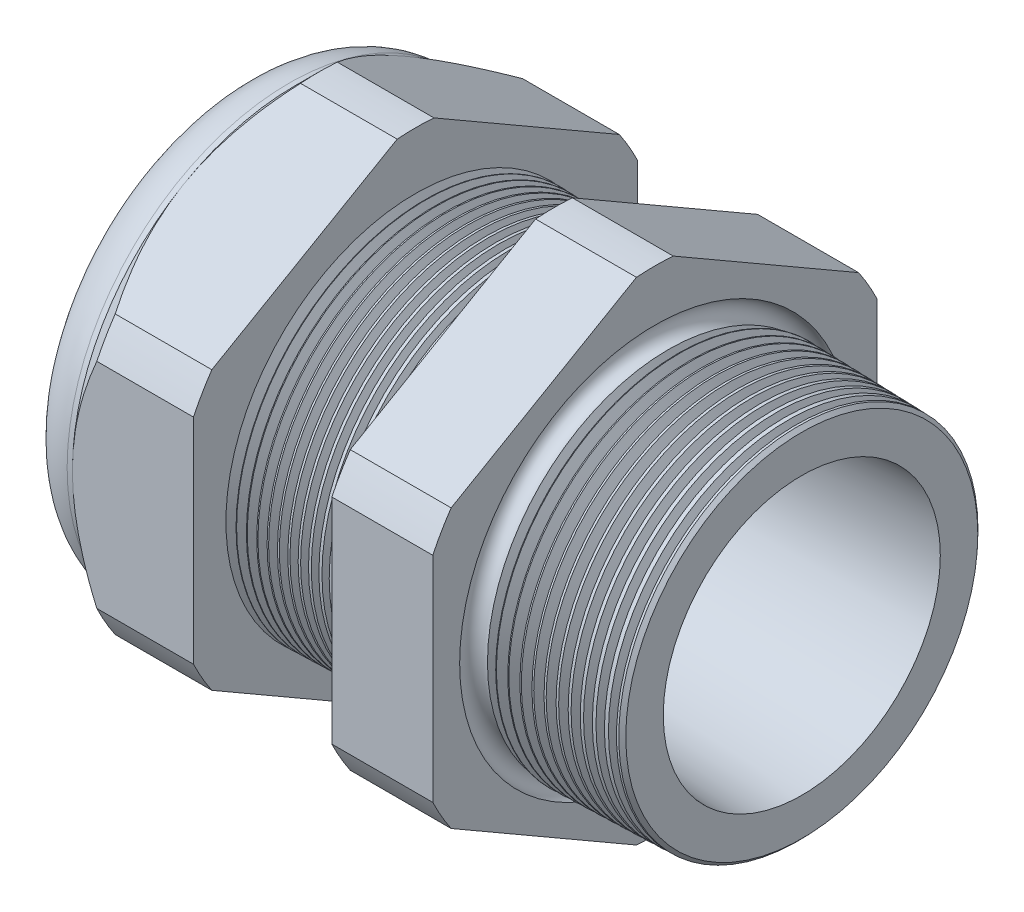
SolidWorks part; units mm, degrees
ref_plane "Front Plane" through (0, 0, 0) normal (0, 0, 1) x (1, 0, 0)
ref_plane "Top Plane" through (0, 0, 0) normal (0, 1, 0) x (1, 0, 0)
ref_plane "Right Plane" through (0, 0, 0) normal (1, 0, 0) x (0, 0, -1)
sketch "Sketch10" plane through (0, 0, 0) normal (0, 0, 1) x (1, 0, 0)
  line L0 (0, 0) -> (-115.3565, 0) construction
  line L1 (-38.862, 9.017) -> (-25.662, 9.017)
  line L2 (3.048, 10.2972) -> (3.048, 13.3452)
  line L3 (-7.874, 13.6312) -> (3.048, 13.3452)
  line L4 (-7.874, 33.02) -> (-7.874, 13.6312)
  line L5 (-7.874, 33.02) -> (-15.374, 33.02)
  line L6 (-15.374, 33.02) -> (-15.374, 13.8276)
  line L7 (-25.662, 14.097) -> (-15.374, 13.8276)
  line L8 (-25.662, 14.097) -> (-25.662, 33.02)
  line L9 (-25.662, 33.02) -> (-34.662, 33.02)
  line L10 (-34.662, 33.02) -> (-34.662, 16.51)
  line L11 (-34.662, 16.51) -> (-38.862, 16.51)
  line L12 (-38.862, 16.51) -> (-38.862, 9.017)
  line L13 (-25.662, 9.017) -> (3.048, 10.2972)
  dimension "D1" = 41.91
  dimension "D2" = 18.034
  dimension "D3" = 1.5
  dimension "D4" = 3.048
  dimension "A" = 28.194
  dimension "D6" = 33.02
  dimension "D8" = 66.04
  dimension "D9" = 4.2
  dimension "D10" = 9
  dimension "D11" = 7.5
  dimension "D" = 10.922
revolve "Revolve2" add sketch "Sketch10" angle 360 about L0
sketch "Sketch12" plane through (-34.662, 0, 0) normal (-1, 0, 0) x (0, 0, 1)
  line L1 (-1.3666, 18.2751) -> (-15.1434, 10.3211)
  line L2 (-16.51, 7.954) -> (-16.51, -7.954)
  line L3 (-15.1434, -10.3211) -> (-1.3666, -18.2751)
  line L4 (1.3666, -18.2751) -> (15.1434, -10.3211)
  line L5 (16.51, -7.954) -> (16.51, 7.954)
  line L6 (15.1434, 10.3211) -> (1.3666, 18.2751)
  circle A0 centre (0, 0) radius 16.51 construction
  arc A1 (1.3666, 18.2751) -> (-1.3666, 18.2751) centre (0, 0) ccw
  arc A2 (-15.1434, 10.3211) -> (-16.51, 7.954) centre (0, 0) ccw
  arc A3 (-16.51, -7.954) -> (-15.1434, -10.3211) centre (0, 0) ccw
  arc A4 (-1.3666, -18.2751) -> (1.3666, -18.2751) centre (0, 0) ccw
  arc A5 (15.1434, -10.3211) -> (16.51, -7.954) centre (0, 0) ccw
  arc A6 (16.51, 7.954) -> (15.1434, 10.3211) centre (0, 0) ccw
  dimension "D2" = 36.6522
  dimension "D1" = 33.02
extrude "Cut-Extrude2" cut sketch "Sketch12" against normal through all flip side to cut
fillet "Fillet4" radius 3.81 1 edges at (-38.862, 0, -16.51)
sketch "Sketch19" plane through (-34.662, 0, 0) normal (-1, 0, 0) x (0, 0, 1)
  line L0 (16.51, 0) -> (16.51, 7.954) construction
  circle A0 centre (0, 0) radius 16.51
extrude "Cut-Extrude3" cut sketch "Sketch19" against normal blind 3.998 draft 45 flip side to cut
chamfer "Chamfer1" distance 0.254 angle 45 1 edges at (3.048, 0, -13.3452)
sketch "Sketch21" plane through (-38.862, 0, 0) normal (-1, 0, 0) x (0, 0, 1)
  circle A0 centre (0, 0) radius 9.017
  circle A2 centre (0, 0) radius 9.017 construction
extrude "plug" add sketch "Sketch21" against normal blind 8.89 separate body
sketch "Sketch22" plane through (-38.862, 0, 0) normal (-1, 0, 0) x (0, 0, 1)
  circle A0 centre (0, 0) radius 8.763
  circle A1 centre (0, 0) radius 9.017 construction
  dimension "D1" = 0.254
extrude "Cut-Extrude4" cut sketch "Sketch22" against normal blind 0.508
sketch "Sketch27" plane through (-38.354, 0, 0) normal (-1, 0, 0) x (0, 0, 1)
  line L0 (-4.3624, 0) -> (4.3624, 0) construction
  circle A0 centre (-6.096, 0) radius 2.54
  circle A1 centre (0, 0) radius 8.763 construction
  dimension "D1" = 0.127
  dimension "holedia" = 5.08
extrude "plugholes" cut sketch "Sketch27" against normal through all
pattern_circular "CirPattern1" count 4 every 72 about axis through (0, 0, 0) along (1, 0, 0) of "plugholes"
sketch "Sketch33" plane through (-38.354, 0, 0) normal (-1, 0, 0) x (0, 0, 1)
  line L0 (-6.096, 0) -> (4.9318, 3.5831) construction
  line L2 (0, 0) -> (-1.923, 5.9184) construction
  circle A0 centre (-1.923, 5.9184) radius 1.905
  dimension "D2" = 3.81
  dimension "D1" = 6.223
sketch "Sketch28" [suppressed] plane through (-29.464, 0, 0) normal (-1, 0, 0) x (0, 0, 1)
  circle A0 centre (0, 0) radius 0.762
  dimension "midholedia" = 5.08
extrude "midhole" [suppressed] cut sketch "Sketch28" against normal through all
sketch "Sketch29" plane through (0, 0, 0) normal (0, 0, 1) x (1, 0, 0)
  line L0 (-25.662, 14.097) -> (-24.929, 14.0778)
  line L1 (-15.374, 13.8276) -> (-25.662, 14.097) construction
  line L2 (-24.929, 14.0778) -> (-25.3121, 13.4526)
  line L3 (-25.3121, 13.4526) -> (-25.662, 14.097)
  dimension "D1" = 60
  dimension "D2" = 60
  dimension "D3" = 0.635
revolve "Cut-Revolve1" cut sketch "Sketch29" angle 360 about axis through (0, 0, 0) along (-1, 0, 0)
pattern_linear "LPattern1" count 14 spacing 0.762 along (1, 0, 0) of "Cut-Revolve1"
sketch "Sketch30" plane through (0, 0, 0) normal (0, 0, 1) x (1, 0, 0)
  line L0 (-7.874, 13.6312) -> (-6.9944, 13.6082)
  line L1 (-7.874, 18.2751) -> (-7.874, 10.3211) construction
  line L2 (2.7941, 13.3519) -> (-7.874, 13.6312) construction
  line L3 (-6.9944, 13.6082) -> (-7.4542, 12.8579)
  line L4 (-7.4542, 12.8579) -> (-7.874, 13.6312)
  dimension "D1" = 60
  dimension "D2" = 60
  dimension "D3" = 0.762
revolve "Cut-Revolve2" cut sketch "Sketch30" angle 360 about axis through (0, 0, 0) along (-1, 0, 0)
pattern_linear "LPattern2" count 12 spacing 0.889 along (1, 0, 0) of "Cut-Revolve2"
sketch "Sketch31" [suppressed] plane through (-38.354, 0, 0) normal (-1, 0, 0) x (0, 0, 1)
  line L0 (-1.905, 1.905) -> (1.905, 1.905)
  line L1 (-1.905, -1.905) -> (1.905, -1.905)
  circle A0 centre (0, 0) radius 1.905 construction
  arc A1 (-1.905, 1.905) -> (-1.905, -1.905) centre (-1.905, 0) ccw
  arc A2 (1.905, 1.905) -> (1.905, -1.905) centre (1.905, 0) cw
extrude "Cut-Extrude5" [suppressed] cut sketch "Sketch31" against normal through all
sketch "Sketch32" plane through (0, 0, 0) normal (0, 0, 1) x (1, 0, 0)
  line L0 (-7.874, 18.2751) -> (-7.874, 10.3211) construction
  circle A0 centre (-7.747, 13.6312) radius 0.889
  dimension "D2" = 1.778
  dimension "D1" = 0.127
revolve "Cut-Revolve3" cut sketch "Sketch32" angle 360 about axis through (0, 0, 0) along (-1, 0, 0)
extrude "Cut-Extrude6" cut sketch "Sketch33" against normal through all
